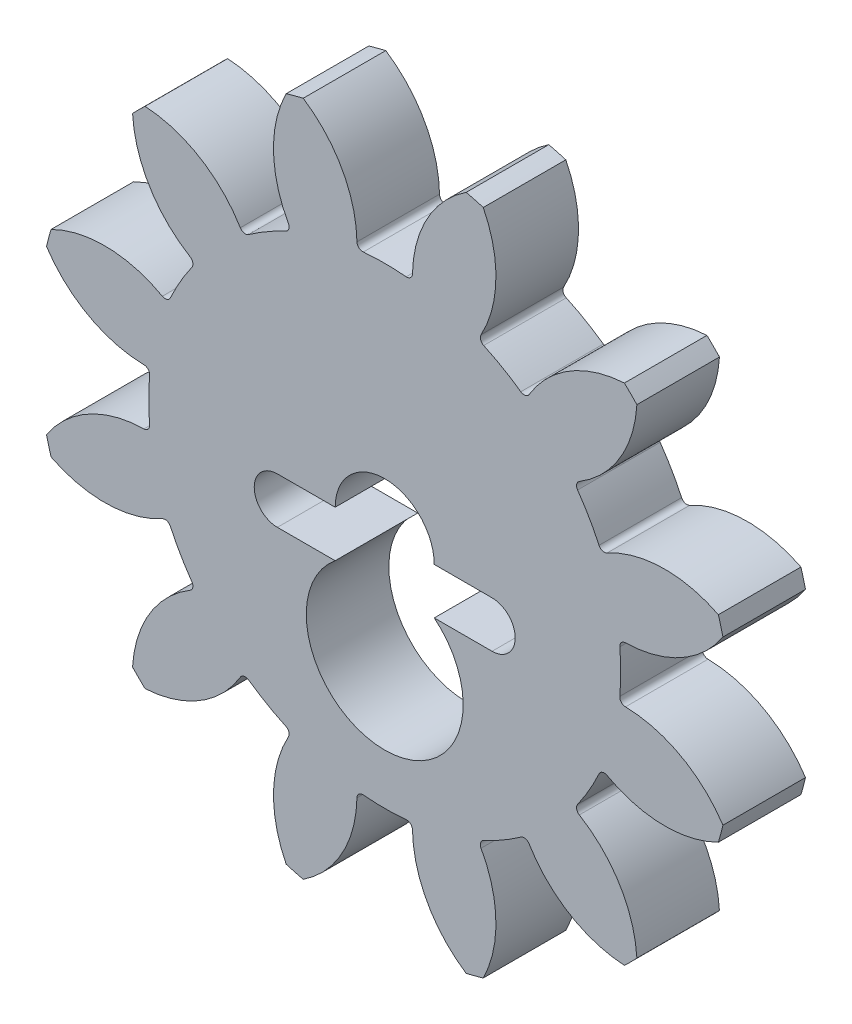
SolidWorks part; units mm, degrees
material "Ti-6Al-4VSolution treated and aged (SS)"
ref_plane "Front Plane" through (0, 0, 0) normal (0, 0, 1) x (1, 0, 0)
ref_plane "Top Plane" through (0, 0, 0) normal (0, 1, 0) x (1, 0, 0)
ref_plane "Right Plane" through (0, 0, 0) normal (1, 0, 0) x (0, 0, -1)
sketch "Sketch1" plane through (0, 0, 0) normal (0, 0, 1) x (1, 0, 0)
  line L4 (-3.302, -1.4244) -> (-1.524, -1.4244)
  line L5 (1.524, -1.4244) -> (3.302, -1.4244)
  line L6 (-1.524, 0) -> (-3.302, 0)
  line L7 (1.524, 0) -> (3.302, 0)
  arc A0 (-7.7573, 7.373) -> (-5.8176, 4.3463) centre (-4.0941, 7.5857) ccw
  arc A1 (-5.8176, 4.3463) -> (-6.6728, 2.865) centre (0, 0) ccw
  arc A2 (-6.6728, 2.865) -> (-10.2638, 3.0315) centre (-8.6165, -0.2472) ccw
  arc A3 (-10.2638, 3.0315) -> (-10.4045, 2.5065) centre (0, 0) ccw
  arc A4 (-10.4045, 2.5065) -> (-7.2113, 0.8553) centre (-7.3385, 4.5224) ccw
  arc A5 (-7.2113, 0.8553) -> (-7.2113, -0.8553) centre (0, 0) ccw
  arc A6 (-7.2113, -0.8553) -> (-10.4045, -2.5065) centre (-7.3385, -4.5224) ccw
  arc A7 (-10.4045, -2.5065) -> (-10.2638, -3.0315) centre (0, 0) ccw
  arc A8 (-10.2638, -3.0315) -> (-6.6728, -2.865) centre (-8.6165, 0.2472) ccw
  arc A9 (-6.6728, -2.865) -> (-5.8176, -4.3463) centre (0, 0) ccw
  arc A10 (-5.8176, -4.3463) -> (-7.7573, -7.373) centre (-4.0941, -7.5857) ccw
  arc A11 (-7.7573, -7.373) -> (-7.373, -7.7573) centre (0, 0) ccw
  arc A12 (-7.373, -7.7573) -> (-4.3463, -5.8176) centre (-7.5857, -4.0941) ccw
  arc A13 (-4.3463, -5.8176) -> (-2.865, -6.6728) centre (0, 0) ccw
  arc A14 (-2.865, -6.6728) -> (-3.0315, -10.2638) centre (0.2472, -8.6165) ccw
  arc A15 (-3.0315, -10.2638) -> (-2.5065, -10.4045) centre (0, 0) ccw
  arc A16 (-2.5065, -10.4045) -> (-0.8553, -7.2113) centre (-4.5224, -7.3385) ccw
  arc A17 (-0.8553, -7.2113) -> (0.8553, -7.2113) centre (0, 0) ccw
  arc A18 (0.8553, -7.2113) -> (2.5065, -10.4045) centre (4.5224, -7.3385) ccw
  arc A19 (2.5065, -10.4045) -> (3.0315, -10.2638) centre (0, 0) ccw
  arc A20 (3.0315, -10.2638) -> (2.865, -6.6728) centre (-0.2472, -8.6165) ccw
  arc A21 (2.865, -6.6728) -> (4.3463, -5.8176) centre (0, 0) ccw
  arc A22 (4.3463, -5.8176) -> (7.373, -7.7573) centre (7.5857, -4.0941) ccw
  arc A23 (7.373, -7.7573) -> (7.7573, -7.373) centre (0, 0) ccw
  arc A24 (7.7573, -7.373) -> (5.8176, -4.3463) centre (4.0941, -7.5857) ccw
  arc A25 (5.8176, -4.3463) -> (6.6728, -2.865) centre (0, 0) ccw
  arc A26 (6.6728, -2.865) -> (10.2638, -3.0315) centre (8.6165, 0.2472) ccw
  arc A27 (10.2638, -3.0315) -> (10.4045, -2.5065) centre (0, 0) ccw
  arc A28 (10.4045, -2.5065) -> (7.2113, -0.8553) centre (7.3385, -4.5224) ccw
  arc A29 (7.2113, -0.8553) -> (7.2113, 0.8553) centre (0, 0) ccw
  arc A30 (7.2113, 0.8553) -> (10.4045, 2.5065) centre (7.3385, 4.5224) ccw
  arc A31 (10.4045, 2.5065) -> (10.2638, 3.0315) centre (0, 0) ccw
  arc A32 (10.2638, 3.0315) -> (6.6728, 2.865) centre (8.6165, -0.2472) ccw
  arc A33 (6.6728, 2.865) -> (5.8176, 4.3463) centre (0, 0) ccw
  arc A34 (5.8176, 4.3463) -> (7.7573, 7.373) centre (4.0941, 7.5857) ccw
  arc A35 (7.7573, 7.373) -> (7.373, 7.7573) centre (0, 0) ccw
  arc A36 (7.373, 7.7573) -> (4.3463, 5.8176) centre (7.5857, 4.0941) ccw
  arc A37 (4.3463, 5.8176) -> (2.865, 6.6728) centre (0, 0) ccw
  arc A38 (2.865, 6.6728) -> (3.0315, 10.2638) centre (-0.2472, 8.6165) ccw
  arc A39 (3.0315, 10.2638) -> (2.5065, 10.4045) centre (0, 0) ccw
  arc A40 (2.5065, 10.4045) -> (0.8553, 7.2113) centre (4.5224, 7.3385) ccw
  arc A41 (0.8553, 7.2113) -> (-0.8553, 7.2113) centre (0, 0) ccw
  arc A42 (-0.8553, 7.2113) -> (-2.5065, 10.4045) centre (-4.5224, 7.3385) ccw
  arc A43 (-2.5065, 10.4045) -> (-3.0315, 10.2638) centre (0, 0) ccw
  arc A44 (-3.0315, 10.2638) -> (-2.865, 6.6728) centre (0.2472, 8.6165) ccw
  arc A45 (-2.865, 6.6728) -> (-4.3463, 5.8176) centre (0, 0) ccw
  arc A46 (-4.3463, 5.8176) -> (-7.373, 7.7573) centre (-7.5857, 4.0941) ccw
  arc A47 (-7.373, 7.7573) -> (-7.7573, 7.373) centre (0, 0) ccw
  arc A48 (1.524, 0) -> (-1.524, 0) centre (0, 0) ccw
  arc A49 (-3.302, 0) -> (-3.302, -1.4244) centre (-3.302, -0.7122) ccw
  arc A50 (-1.524, -1.4244) -> (1.524, -1.4244) centre (0, -3.2952) ccw
  arc A51 (3.302, -1.4244) -> (3.302, 0) centre (3.302, -0.7122) ccw
  dimension "D1" = 3.048
  dimension "D2" = 1.778
  dimension "D3" = 4.826
  dimension "D4" = 1.778
extrude "Boss-Extrude1" add sketch "Sketch1" along normal blind 2.54 contours A48 A50
fillet "Fillet1" radius 0.1778 24 edges at (6.6728, -2.865, 1.27) (5.8176, -4.3463, 1.27) (4.3463, -5.8176, 1.27) (2.865, -6.6728, 1.27) (0.8553, -7.2113, 1.27) (-0.8553, -7.2113, 1.27) (-2.865, -6.6728, 1.27) (-4.3463, -5.8176, 1.27) (-5.8176, -4.3463, 1.27) (-6.6728, -2.865, 1.27) (-7.2113, -0.8553, 1.27) (-7.2113, 0.8553, 1.27) (-6.6728, 2.865, 1.27) (-5.8176, 4.3463, 1.27) (7.2113, -0.8553, 1.27) (7.2113, 0.8553, 1.27) (6.6728, 2.865, 1.27) (5.8176, 4.3463, 1.27) (2.865, 6.6728, 1.27) (4.3463, 5.8176, 1.27) (-0.8553, 7.2113, 1.27) (0.8553, 7.2113, 1.27) (-4.3463, 5.8176, 1.27) (-2.865, 6.6728, 1.27)
